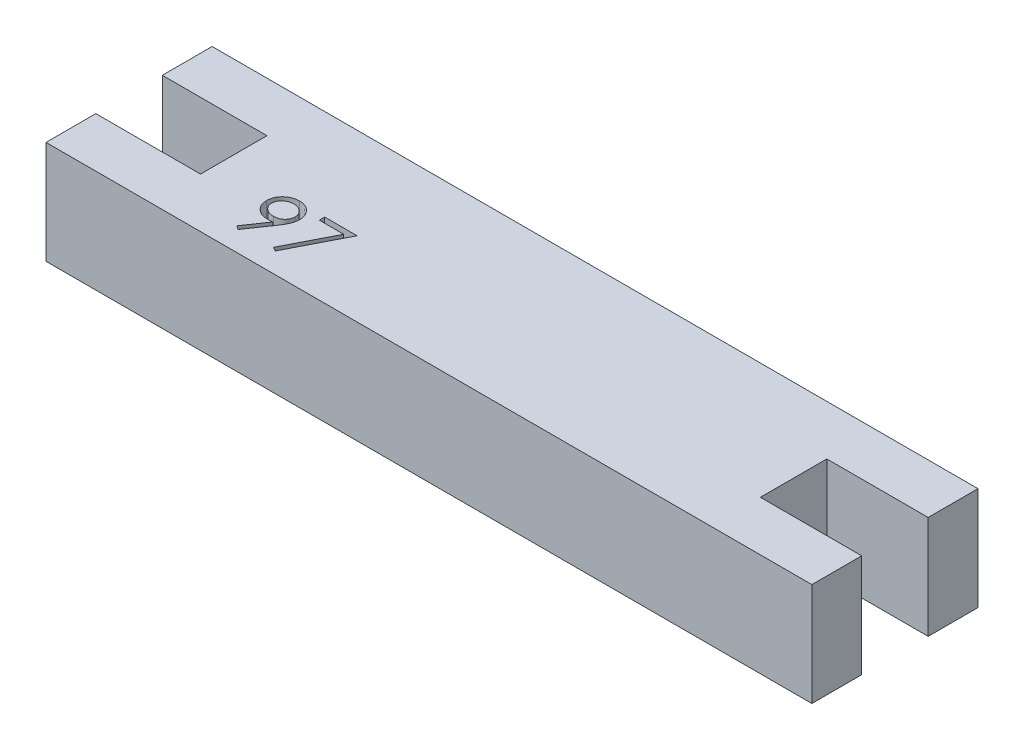
SolidWorks part; units mm, degrees
ref_plane "Front Plane" through (0, 0, 0) normal (0, 0, 1) x (1, 0, 0)
ref_plane "Top Plane" through (0, 0, 0) normal (0, 1, 0) x (1, 0, 0)
ref_plane "Right Plane" through (0, 0, 0) normal (1, 0, 0) x (0, 0, -1)
sketch "Sketch1" plane through (0, 0, 0) normal (0, 1, 0) x (1, 0, 0)
  line L0 (0, 0) -> (33.7, 0)
  line L1 (33.8, 3) -> (33.8, 7)
  line L2 (33.7, 10) -> (0, 10)
  line L3 (0.1, 7) -> (0.1, 3)
  line L4 (0, 10) -> (-6.2, 10)
  line L5 (-6.2, 10) -> (-6.2, 7)
  line L6 (-6.2, 0) -> (0, 0)
  line L7 (33.7, 0) -> (39.9, 0)
  line L8 (39.9, 0) -> (39.9, 3)
  line L9 (39.9, 10) -> (33.7, 10)
  line L10 (-6.2, 7) -> (0.1, 7)
  line L11 (-6.2, 3) -> (0.1, 3)
  line L12 (33.8, 7) -> (39.9, 7)
  line L13 (33.8, 3) -> (39.9, 3)
  line L14 (-6.2, 3) -> (-6.2, 0)
  line L15 (39.9, 7) -> (39.9, 10)
  dimension "D1" = 33.7
  dimension "D2" = 10
  dimension "D3" = 6.2
  dimension "D4" = 6.2
  dimension "D5" = 3
  dimension "D6" = 3
extrude "Boss-Extrude1" add sketch "Sketch1" along normal blind 6.2
sketch "Sketch2" plane through (0, 6.2, 0) normal (0, 1, 0) x (1, 0, 0)
  text T0 "97"
  point P1 (8.5056, 4.5169)
  point P2 (3.3082, 1.3222)
extrude "Cut-Extrude1" cut sketch "Sketch2" against normal blind 1
